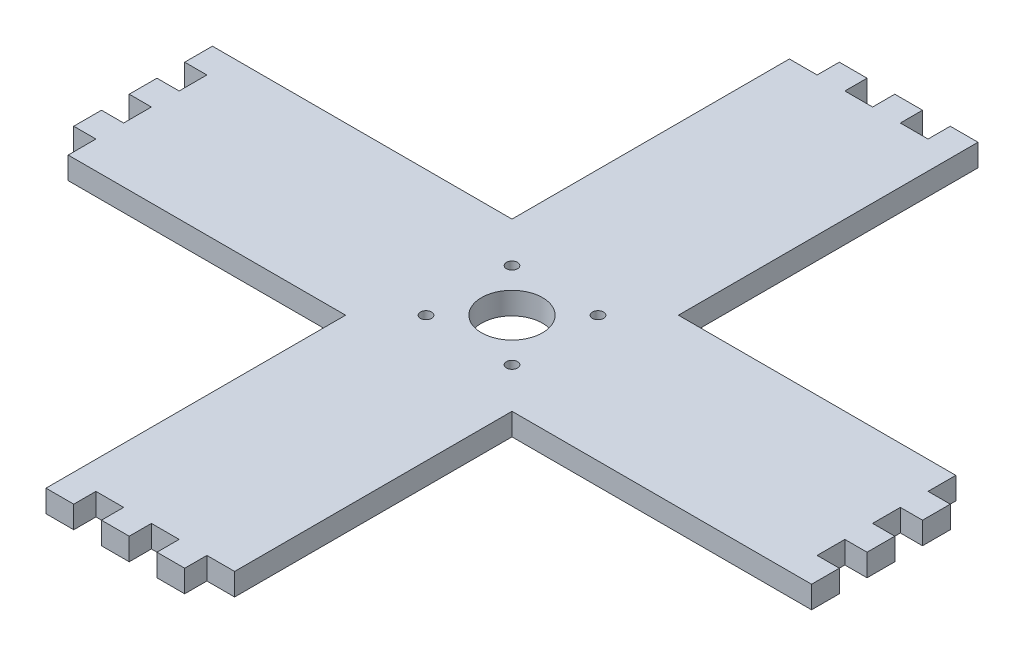
SolidWorks part; units mm, degrees
ref_plane "前视基准面" through (0, 0, 0) normal (0, 0, 1) x (1, 0, 0)
ref_plane "上视基准面" through (0, 0, 0) normal (0, 1, 0) x (1, 0, 0)
ref_plane "右视基准面" through (0, 0, 0) normal (1, 0, 0) x (0, 0, -1)
sketch "草图1" plane through (0, 0, 0) normal (0, 1, 0) x (1, 0, 0)
  line L0 (-130, -30) -> (-30, -30)
  line L1 (-138, -20) -> (-138, -10)
  line L2 (138, -30) -> (138, -20)
  line L3 (-138, 30) -> (-30, 30)
  line L4 (30, 30) -> (130, 30)
  line L5 (30, -30) -> (138, -30)
  line L6 (-30, -138) -> (-30, -30)
  line L7 (-30, -138) -> (-20, -138)
  line L8 (-20, 138) -> (-10, 138)
  line L9 (30, -130) -> (30, -30)
  line L10 (0, 138) -> (10, 138)
  line L11 (20, 138) -> (30, 138)
  line L12 (-20, 138) -> (-20, 130)
  line L13 (-30, 130) -> (-20, 130)
  line L16 (30, 30) -> (30, 138)
  line L17 (-30, 30) -> (-30, 130)
  line L19 (-10, 138) -> (-10, 130)
  line L22 (-10, 130) -> (0, 130)
  line L23 (0, 138) -> (0, 130)
  line L26 (-20, -138) -> (-20, -130)
  line L27 (10, 138) -> (10, 130)
  line L28 (138, 10) -> (138, 20)
  line L30 (10, 130) -> (20, 130)
  line L31 (20, 138) -> (20, 130)
  line L34 (138, -10) -> (138, 0)
  line L36 (-20, 130) -> (-10, 130) [skipped]
  line L37 (0, 130) -> (10, 130) [skipped]
  line L38 (20, 130) -> (30, 130) [skipped]
  line L40 (-20, -130) -> (-10, -130)
  line L41 (-10, -138) -> (-10, -130)
  line L44 (-10, -138) -> (0, -138)
  line L45 (0, -138) -> (0, -130)
  line L46 (130, 30) -> (130, 20)
  line L48 (0, -130) -> (10, -130)
  line L49 (10, -138) -> (10, -130)
  line L53 (20, -138) -> (20, -130)
  line L54 (10, -138) -> (20, -138)
  line L56 (20, -130) -> (30, -130)
  line L57 (138, 20) -> (130, 20)
  line L58 (30, -138) -> (30, -130) [skipped]
  line L59 (20, -138) -> (30, -138) [skipped]
  line L60 (0, -138) -> (10, -138) [skipped]
  line L63 (-20, -138) -> (-10, -138) [skipped]
  line L64 (-138, 0) -> (-138, 10)
  line L65 (138, 10) -> (130, 10)
  line L66 (-138, 20) -> (-138, 30)
  line L68 (130, 10) -> (130, 0)
  line L69 (138, 0) -> (130, 0)
  line L72 (-130, -30) -> (-130, -20)
  line L73 (138, -10) -> (130, -10)
  line L75 (138, -20) -> (130, -20)
  line L76 (130, -10) -> (130, -20)
  line L80 (-138, -20) -> (-130, -20)
  line L81 (130, 20) -> (130, 10) [skipped]
  line L82 (130, 0) -> (130, -10) [skipped]
  line L83 (130, -20) -> (130, -30) [skipped]
  line L85 (-138, -10) -> (-130, -10)
  line L89 (-138, 0) -> (-130, 0)
  line L90 (-130, -10) -> (-130, 0)
  line L93 (-138, 10) -> (-130, 10)
  line L97 (-138, 20) -> (-130, 20)
  line L98 (-130, 10) -> (-130, 20)
  line L103 (-130, -20) -> (-130, -10) [skipped]
  line L104 (-130, 0) -> (-130, 10) [skipped]
  line L105 (-130, 20) -> (-130, 30) [skipped]
  line L106 (138, -30) -> (130, -30) [skipped]
  line L107 (-138, 30) -> (-130, 30) [skipped]
  line L108 (30, 138) -> (30, 130) [skipped]
  circle A0 centre (0, 0) radius 11
  circle A1 centre (-15.5, 15.5) radius 2
  circle A2 centre (15.5, 15.5) radius 2
  circle A3 centre (-15.5, -15.5) radius 2
  circle A4 centre (15.5, -15.5) radius 2
  point P1 (0, 0)
  point P2 (0, 0)
  dimension "D1" = 6
  dimension "D2" = 6
  dimension "D3" = 6
  dimension "D4" = 6
extrude "凸台-拉伸1" add sketch "草图1" along normal blind 8
